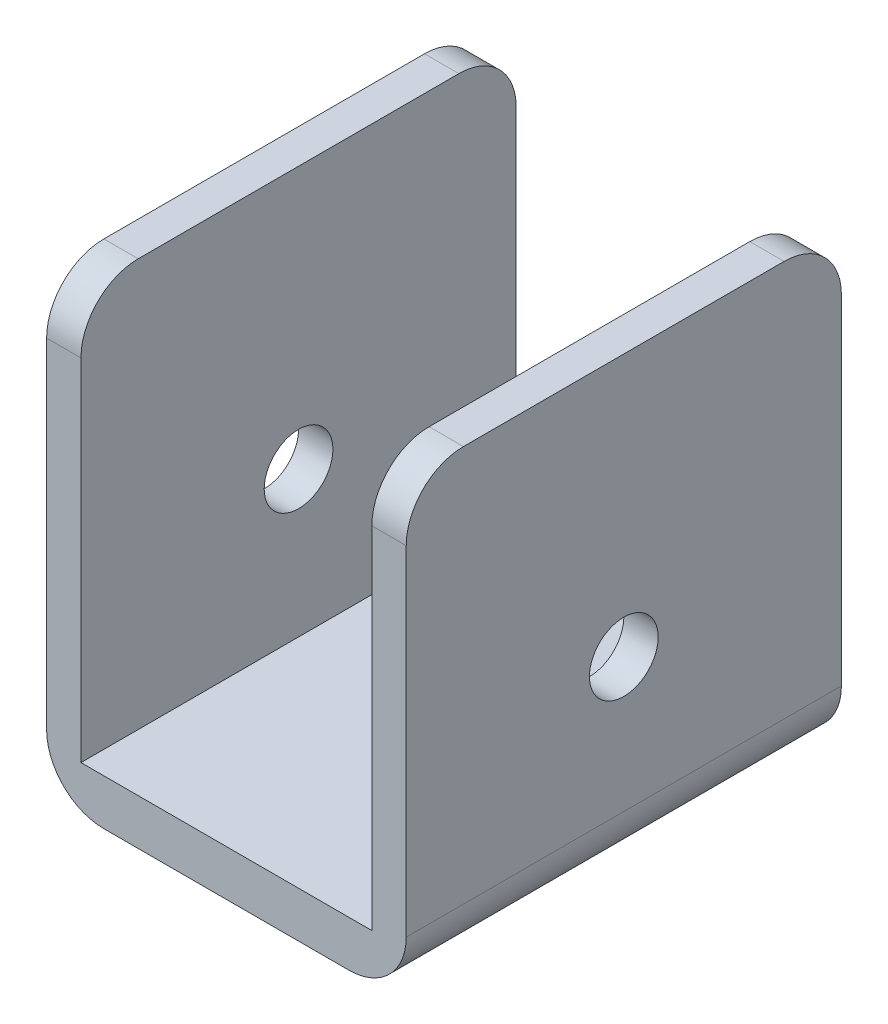
SolidWorks part; units mm, degrees
ref_plane "Front Plane" through (0, 0, 0) normal (0, 0, 1) x (1, 0, 0)
ref_plane "Top Plane" through (0, 0, 0) normal (0, 1, 0) x (1, 0, 0)
ref_plane "Right Plane" through (0, 0, 0) normal (1, 0, 0) x (0, 0, -1)
sketch "Sketch1" plane through (0, 0, 0) normal (0, 0, 1) x (1, 0, 0)
  line L0 (-15.7, 39.6) -> (-12.7, 39.6)
  line L1 (-12.7, 39.6) -> (-12.7, 4)
  line L2 (-12.7, 4) -> (12.7, 4)
  line L3 (-15.7, 39.6) -> (-15.7, 0)
  line L4 (-15.7, 0) -> (15.7, 0)
  line L5 (0, 33.2714) -> (0, -36.0595) construction
  line L6 (15.7, 39.6) -> (15.7, 0)
  line L7 (12.7, 39.6) -> (12.7, 4)
  line L8 (15.7, 39.6) -> (12.7, 39.6)
  point P11 (0, 0)
  point P13 (0, 4)
  dimension "D1" = 12.7
  dimension "D2" = 4
  dimension "D3" = 3
  dimension "D4" = 39.6
extrude "Boss-Extrude1" add sketch "Sketch1" along normal mid plane 38
sketch "Sketch2" plane through (15.7, 0, 0) normal (1, 0, 0) x (0, 0, -1)
  line L0 (0, 43.2613) -> (0, -4.7877) construction
  line L3 (-19, 0) -> (19, 0) construction
  circle A6 centre (0, 16.7) radius 3
  dimension "D8" = 6
  dimension "D7" = 16.7
extrude "Cut-Extrude1" cut sketch "Sketch2" against normal through all
fillet "Fillet1" radius 5 6 edges at (-15.7, 0, 0) (15.7, 0, 0) (-14.2, 39.6, 19) (-14.2, 39.6, -19) (14.2, 39.6, -19) (14.2, 39.6, 19)
